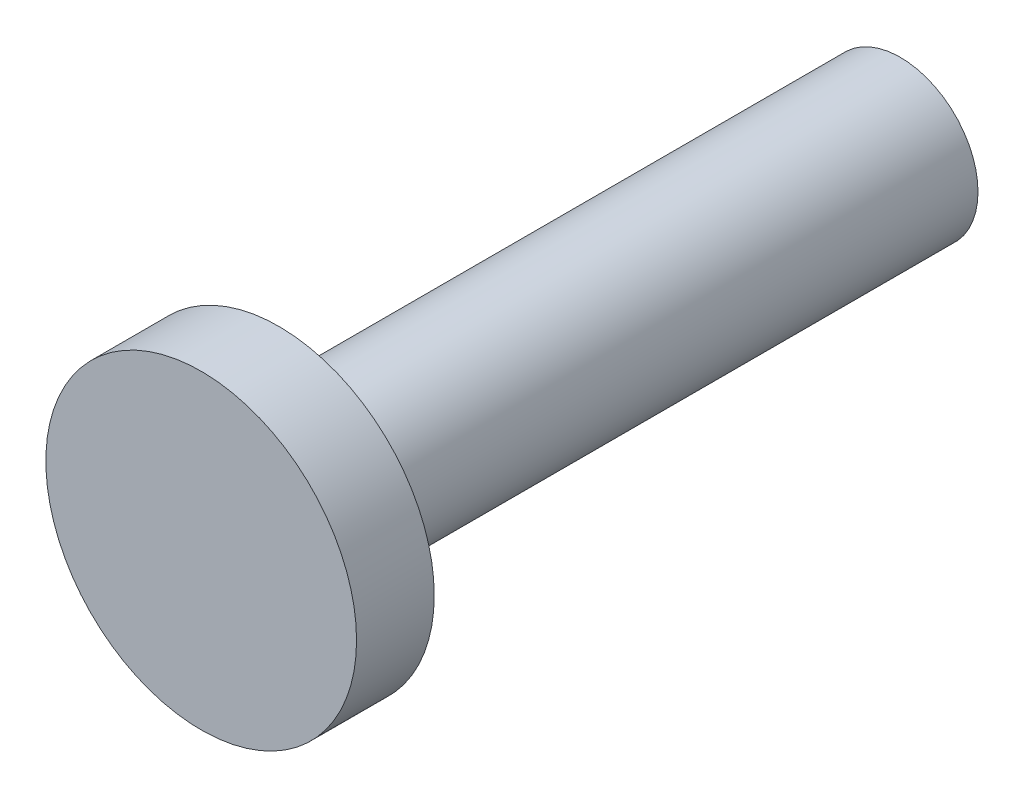
SolidWorks part; units mm, degrees
ref_plane "Front Plane" through (0, 0, 0) normal (0, 0, 1) x (1, 0, 0)
ref_plane "Top Plane" through (0, 0, 0) normal (0, 1, 0) x (1, 0, 0)
ref_plane "Right Plane" through (0, 0, 0) normal (1, 0, 0) x (0, 0, -1)
sketch "Sketch1" plane through (0, 0, 0) normal (0, 0, 1) x (1, 0, 0)
  circle A0 centre (0, 0) radius 1
extrude "Boss-Extrude1" add sketch "Sketch1" along normal blind 8 contours A0
sketch "Sketch2" plane through (0, 0, 8) normal (0, 0, 1) x (1, 0, 0)
  circle A0 centre (0, 0) radius 2
extrude "Boss-Extrude2" add sketch "Sketch2" along normal blind 1
